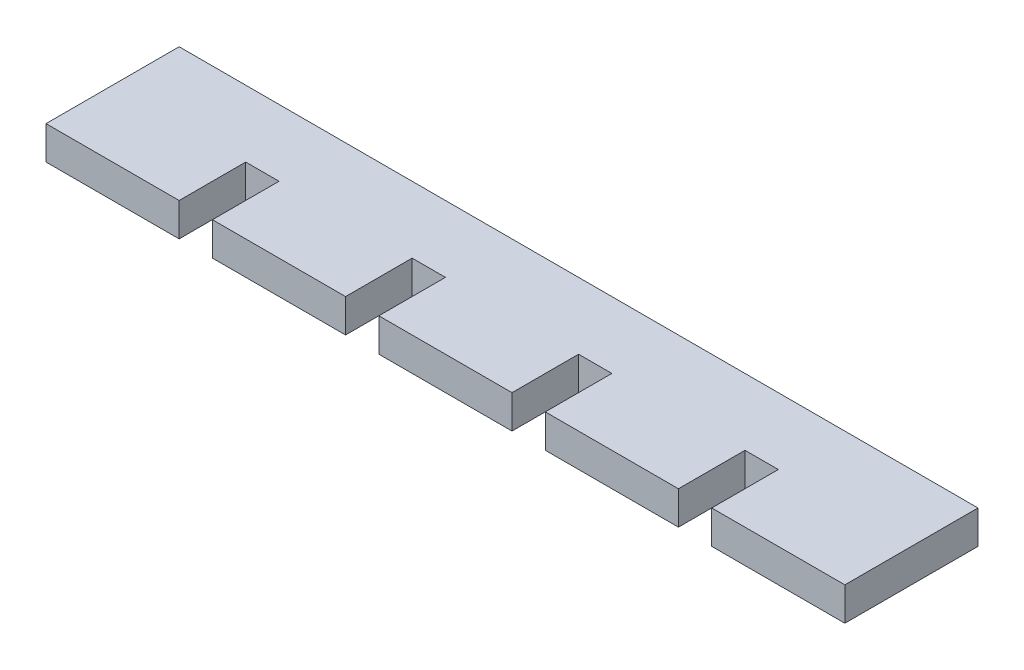
SolidWorks part; units mm, degrees
ref_plane "Front Plane" through (0, 0, 0) normal (0, 0, 1) x (1, 0, 0)
ref_plane "Top Plane" through (0, 0, 0) normal (0, 1, 0) x (1, 0, 0)
ref_plane "Right Plane" through (0, 0, 0) normal (1, 0, 0) x (0, 0, -1)
sketch "Sketch1" plane through (0, 0, 0) normal (0, 1, 0) x (1, 0, 0)
  line L1 (0, 0) -> (76.2, 0)
  line L2 (0, 0) -> (0, -12.7)
  line L3 (0, -12.7) -> (76.2, -12.7)
  line L4 (76.2, 0) -> (76.2, -12.7)
extrude "Boss-Extrude1" add sketch "Sketch1" along normal blind 3.175
sketch "Sketch3" plane through (0, 3.175, 0) normal (0, 1, 0) x (1, 0, 0)
  line L0 (0, 0) -> (0, -12.7) construction
  line L5 (76.2, 0) -> (0, 0) construction
  line L6 (0, -12.7) -> (76.2, -12.7) construction
  line L7 (0, -6.35) -> (12.7, -6.35) construction
  line L8 (12.7, 0) -> (12.7, -12.7) construction
  line L9 (12.7, -6.35) -> (15.875, -6.35) construction
  line L10 (15.875, 0) -> (15.875, -12.7) construction
sketch "Sketch4" plane through (0, 3.175, 0) normal (0, 1, 0) x (1, 0, 0)
  line L0 (12.7, -6.35) -> (12.7, -12.7)
  line L1 (12.7, -6.35) -> (15.875, -6.35)
  line L2 (15.875, -6.35) -> (15.875, -12.7)
  line L3 (12.7, -12.7) -> (15.875, -12.7)
extrude "Cut-Extrude1" cut sketch "Sketch4" against normal through all
pattern_linear "LPattern1" count 4 spacing 15.875 along (1, 0, 0) of "Cut-Extrude1"
sketch "Sketch5" plane through (0, 3.175, 0) normal (0, 1, 0) x (1, 0, 0)
  line L2 (0, -12.7) -> (12.7, -12.7) construction
  line L3 (6.35, -9.7) -> (9.35, -9.7)
  line L9 (9.35, -9.7) -> (9.35, -12.7)
  line L10 (9.35, -12.7) -> (3.35, -12.7)
  line L11 (3.35, -12.7) -> (3.35, -9.7)
  line L12 (3.35, -9.7) -> (6.35, -9.7)
extrude "Cut-Extrude2" [suppressed] cut sketch "Sketch5" against normal through all
pattern_linear "LPattern2" [suppressed] count 5 spacing 15.875
